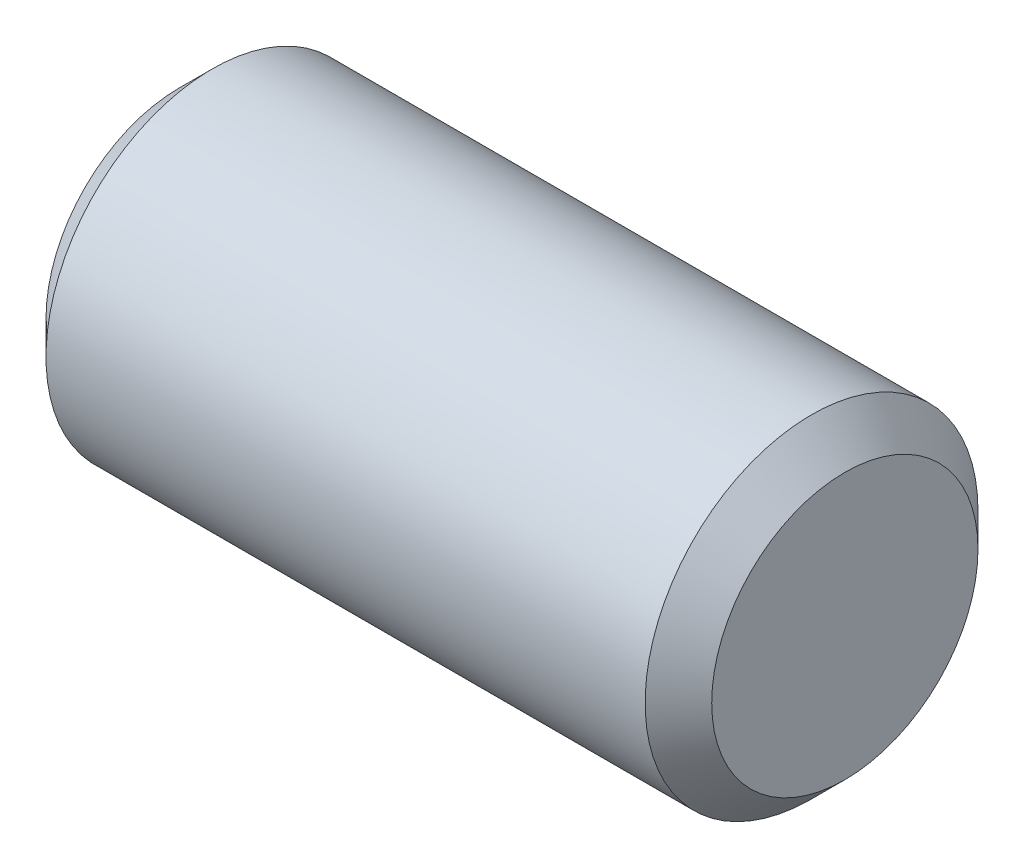
SolidWorks part; units mm, degrees
ref_plane "Front Plane" through (0, 0, 0) normal (0, 0, 1) x (1, 0, 0)
ref_plane "Top Plane" through (0, 0, 0) normal (0, 1, 0) x (1, 0, 0)
ref_plane "Right Plane" through (0, 0, 0) normal (1, 0, 0) x (0, 0, -1)
sketch "Sketch1" plane through (0, 0, 0) normal (0, 0, 1) x (1, 0, 0)
  line L0 (-3.175, 0) -> (3.175, 0) construction
  line L1 (-3.175, 1.5875) -> (-3.175, -1.5875) construction
  line L2 (3.175, 1.5875) -> (3.175, -1.5875) construction
  dimension "Diameter" = 3.175
  dimension "Length" = 6.35
sketch "Sketch2" plane through (0, 0, 0) normal (1, 0, 0) x (0, 0, -1)
  circle A0 centre (0, 0) radius 1.5875
extrude "Extrude1" add sketch "Sketch2" against normal up to vertex (3.175 mm away) and the other way up to vertex (3.175 mm away) up to point (-3.175, 0, 0) other way up to point (3.175, 0, 0)
chamfer "Chamfer1" distance 0.3175 angle 45 2 edges at (3.175, 0, -1.5875) (-3.175, 0, -1.5875)
equation "\"D1@Chamfer1\" = \"Diameter@Sketch1\"*.1"
